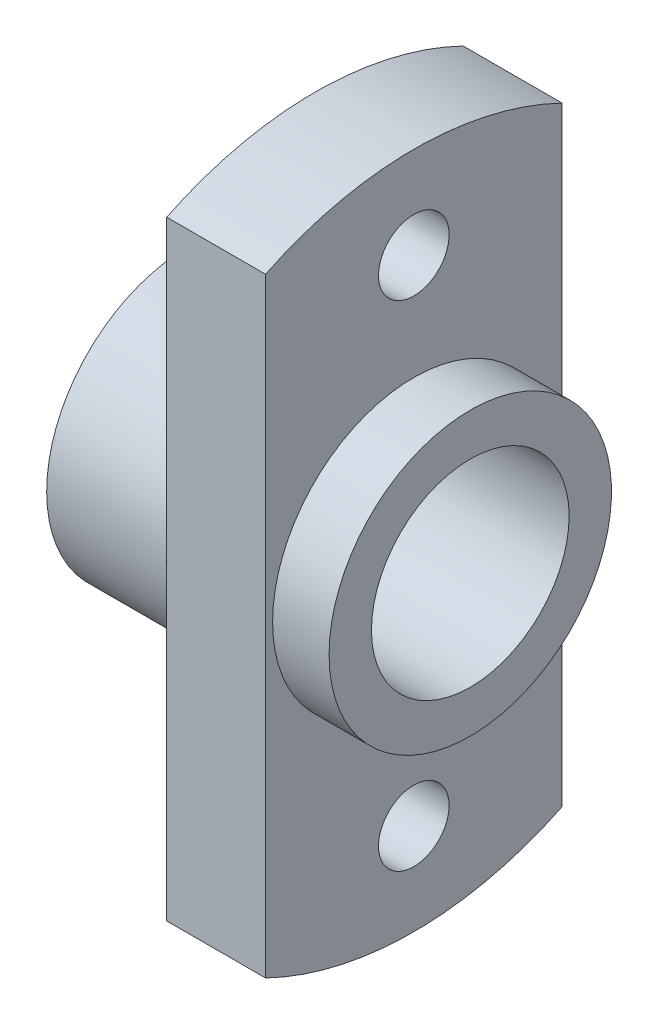
SolidWorks part; units mm, degrees
material "Brass"
ref_plane "Front Plane" through (0, 0, 0) normal (0, 0, 1) x (1, 0, 0)
ref_plane "Top Plane" through (0, 0, 0) normal (0, 1, 0) x (1, 0, 0)
ref_plane "Right Plane" through (0, 0, 0) normal (1, 0, 0) x (0, 0, -1)
sketch "Sketch1" plane through (0, 0, 0) normal (0, 0, 1) x (1, 0, 0)
  line L0 (0, 0) -> (0, 5)
  line L1 (0, 5) -> (4.5, 5)
  line L2 (4.5, 5) -> (4.5, 12)
  line L3 (4.5, 12) -> (8, 12)
  line L4 (8, 12) -> (8, 5)
  line L5 (8, 5) -> (10, 5)
  line L6 (10, 5) -> (10, 0)
  line L7 (-27.2262, 0) -> (104.082, 0) construction
  line L8 (0, 0) -> (10, 0)
  dimension "D1" = 24
  dimension "D2" = 10
  dimension "D3" = 10
  dimension "D4" = 10
  dimension "D5" = 3.5
  dimension "D6" = 2
revolve "Revolve1" add sketch "Sketch1" angle 360 about L7
hole_wizard "M8x1.0 Tapped Hole1" positions "Sketch4" profile "Sketch5" tap size "M8x1.0" standard "ANSI Metric" end condition through all
sketch "Sketch4" plane through (10, 0, 0) normal (1, 0, 0) x (0, 0, -1)
  point P0 (0, 0)
sketch "Sketch5" plane through (10, 0, 0) normal (0, 1, 0) x (0, 0, -1)
  line L0 (0, 0) -> (0, 10)
  line L1 (0, 10) -> (3.5, 10)
  line L2 (3.5, 10) -> (3.5, 0)
  line L5 (3.5, 0) -> (0, 0)
  line L11 (0, -6.35) -> (0, 107.95) construction
  dimension "Thru Tap Drill Dia." = 7
  dimension "Thru Tap Drill Depth" = 10
cosmetic thread "Hole Thread1" parameters "D2"=8
sketch "Sketch6" plane through (8, 0, 0) normal (1, 0, 0) x (0, 0, -1)
  line L0 (-5.25, -13.2689) -> (5.25, -13.2689) construction
  line L1 (5.25, 14.9425) -> (22.7223, 14.9425)
  line L2 (5.25, 14.9425) -> (5.25, -14.9425)
  line L3 (5.25, -14.9425) -> (22.7223, -14.9425)
  line L4 (22.7223, 14.9425) -> (22.7223, -14.9425)
  line L5 (-14.0959, 14.9425) -> (-5.25, 14.9425)
  line L6 (-14.0959, 14.9425) -> (-14.0959, -14.9425)
  line L7 (-14.0959, -14.9425) -> (-5.25, -14.9425)
  line L8 (-5.25, 14.9425) -> (-5.25, -14.9425)
  line L9 (0, 8.75) -> (0, -8.75) construction
  circle A0 centre (0, 8.75) radius 1.25
  circle A1 centre (0, -8.75) radius 1.25
  point P8 (-5.25, 0)
  point P12 (0, -13.2689)
  point P17 (0, 0)
  dimension "D2" = 2.5
  dimension "D1" = 10.5
  dimension "D3" = 17.5
extrude "Cut-Extrude1" cut sketch "Sketch6" against normal up to vertex (3.5 mm away)
